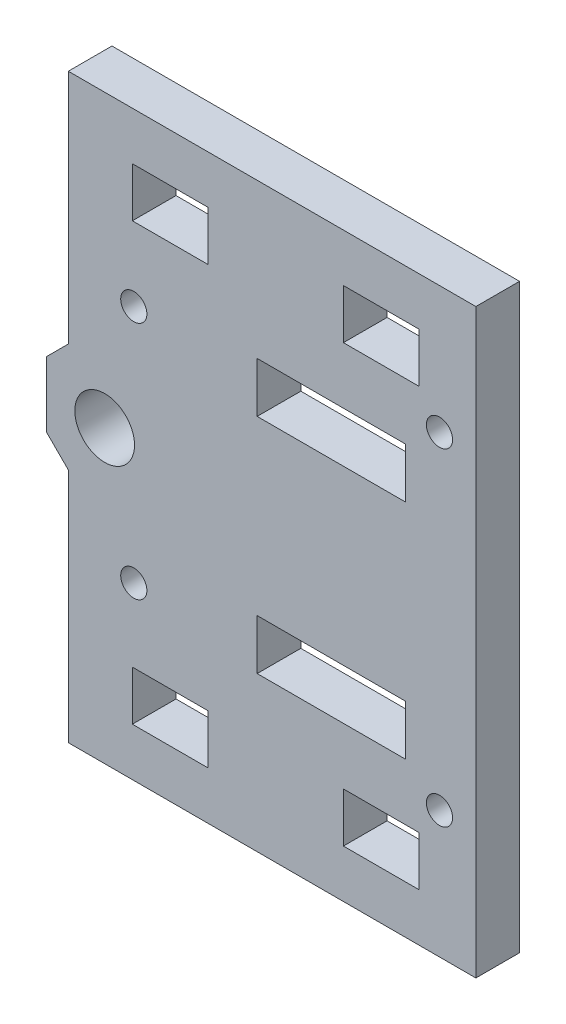
SolidWorks part; units mm, degrees
ref_plane "Plano frontal" through (0, 0, 0) normal (0, 0, 1) x (1, 0, 0)
ref_plane "Plano superior" through (0, 0, 0) normal (0, 1, 0) x (1, 0, 0)
ref_plane "Plano direito" through (0, 0, 0) normal (1, 0, 0) x (0, 0, -1)
sketch "Model" plane through (0, 0, 0) normal (0, 0, 1) x (1, 0, 0)
  line L0 (86.2842, 87.3657) -> (30.2842, 87.3657)
  line L1 (56.2332, 28.6657) -> (56.2332, 35.5657)
  line L2 (76.6016, 35.5657) -> (76.6016, 28.6657)
  line L3 (49.4842, 14.0657) -> (49.4842, 20.8657)
  line L4 (39.0842, 20.8657) -> (49.4842, 20.8657)
  line L5 (39.0842, 14.0657) -> (39.0842, 20.8657)
  line L6 (49.4842, 14.0657) -> (39.0842, 14.0657)
  line L7 (49.4842, 73.9657) -> (49.4842, 80.7657)
  line L8 (39.0842, 80.7657) -> (49.4842, 80.7657)
  line L9 (39.0842, 73.9657) -> (39.0842, 80.7657)
  line L10 (49.4842, 73.9657) -> (39.0842, 73.9657)
  line L11 (56.2332, 66.1657) -> (76.6016, 66.1657)
  line L12 (56.2332, 59.2657) -> (76.6016, 59.2657)
  line L13 (56.2332, 35.5657) -> (76.6016, 35.5657)
  line L14 (56.2332, 28.6657) -> (76.6016, 28.6657)
  line L15 (27.2842, 42.9266) -> (30.2842, 39.9266)
  line L16 (27.2842, 51.9048) -> (27.2842, 42.9266)
  line L17 (27.2842, 51.9048) -> (30.2842, 54.9048)
  line L18 (30.2842, 54.9048) -> (30.2842, 87.3657)
  line L19 (76.6016, 66.1657) -> (76.6016, 59.2657)
  line L20 (56.2332, 59.2657) -> (56.2332, 66.1657)
  line L21 (86.2842, 87.3657) -> (86.2842, 7.4657)
  line L22 (30.2842, 7.4657) -> (30.2842, 39.9266)
  line L23 (86.2842, 7.4657) -> (30.2842, 7.4657)
  line L24 (68.0842, 20.8657) -> (78.4842, 20.8657)
  line L25 (78.4842, 20.8657) -> (78.4842, 14.0657)
  line L26 (78.4842, 14.0657) -> (68.0842, 14.0657)
  line L27 (68.0842, 14.0657) -> (68.0842, 20.8657)
  line L28 (68.0842, 80.7657) -> (78.4842, 80.7657)
  line L29 (78.4842, 80.7657) -> (78.4842, 73.9657)
  line L30 (78.4842, 73.9657) -> (68.0842, 73.9657)
  line L31 (68.0842, 73.9657) -> (68.0842, 80.7657)
  circle A0 centre (39.2842, 30.9657) radius 1.8
  circle A1 centre (81.2842, 24.9157) radius 1.8
  circle A2 centre (81.2842, 69.9157) radius 1.8
  circle A3 centre (39.2842, 63.8657) radius 1.8
  circle A4 centre (35.2842, 47.4157) radius 4.1
extrude "Ressalto-extrusão1" add sketch "Model" along normal blind 6
ref_plane "Plano1" through (0, 62.7157, 0) normal (0, -1, 0) x (-1, 0, 0)
ref_plane "Plano2" through (0, 32.1157, 0) normal (0, 1, 0) x (1, 0, 0)
ref_plane "Plano3" through (66.4174, 0, 0) normal (1, 0, 0) x (0, 0, -1)
ref_plane "Plano4" through (0, 77.3657, 0) normal (0, 1, 0) x (1, 0, 0)
ref_plane "Plano5" through (0, 17.4657, 0) normal (0, -1, 0) x (-1, 0, 0)
ref_plane "Plano6" through (58.7842, 0, 0) normal (1, 0, 0) x (0, 0, -1)
ref_plane "Plano7" through (0, 47.4157, 0) normal (0, -1, 0) x (-1, 0, 0)
